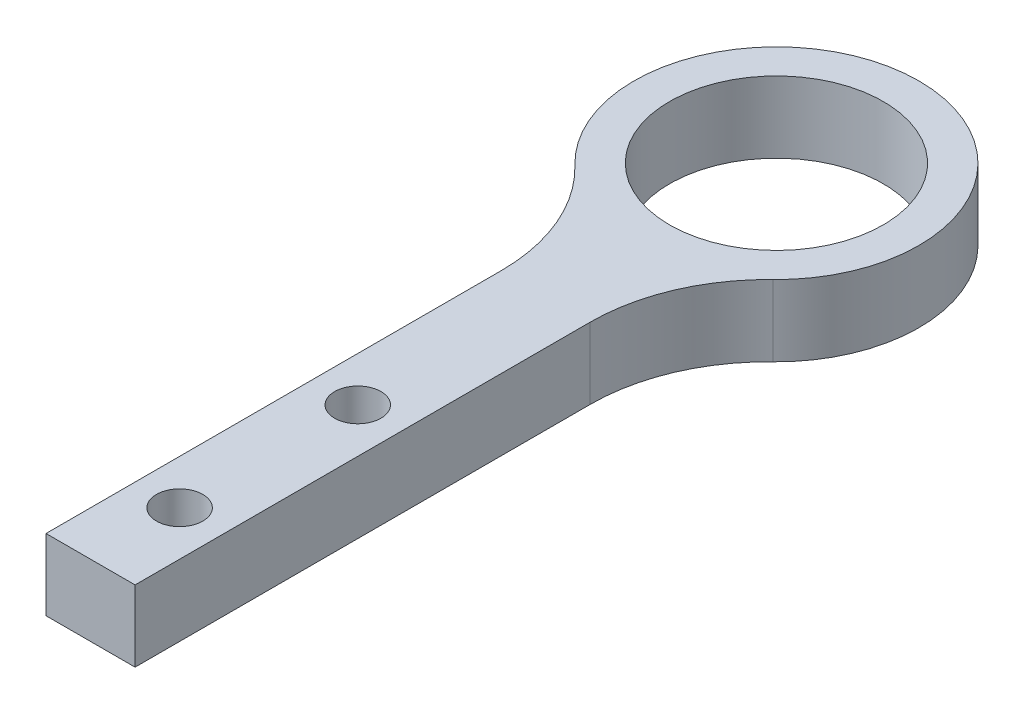
SolidWorks part; units mm, degrees
material "Nylon 101"
ref_plane "Front Plane" through (0, 0, 0) normal (0, 0, 1) x (1, 0, 0)
ref_plane "Top Plane" through (0, 0, 0) normal (0, 1, 0) x (1, 0, 0)
ref_plane "Right Plane" through (0, 0, 0) normal (1, 0, 0) x (0, 0, -1)
sketch "Sketch1" plane through (0, 0, 0) normal (0, 1, 0) x (1, 0, 0)
  line L2 (-2.5, -12.9518) -> (-2.5, -38.5)
  line L3 (-2.5, -38.5) -> (2.5, -38.5)
  line L4 (2.5, -12.9518) -> (2.5, -38.5)
  circle A0 centre (0, 0) radius 6
  arc A1 (5.5556, -5.7564) -> (-5.5556, -5.7564) centre (0, 0) ccw
  arc A4 (5.5556, -5.7564) -> (2.5, -12.9518) centre (12.5, -12.9518) ccw
  arc A5 (-5.5556, -5.7564) -> (-2.5, -12.9518) centre (-12.5, -12.9518) cw
  dimension "D1" = 2
  dimension "D2" = 12
  dimension "D4" = 38.5
  dimension "D5" = 10
  dimension "D3" = 5
extrude "Boss-Extrude1" add sketch "Sketch1" along normal blind 4
sketch "Sketch2" plane through (2.5, 0, 0) normal (0, 1, 0) x (0, 0, -1)
  circle A2 centre (-33.5, 2.5) radius 0.8 construction
  circle A3 centre (-23.5, 2.5) radius 0.8 construction
  circle A4 centre (-33.5, 2.5) radius 0.8
  circle A5 centre (-23.5, 2.5) radius 0.8
hole_wizard "CSK for M2 Flat Head Machine Screw1" positions "Sketch3" profile "Sketch4" countersink size "M2" standard "ANSI Metric" end condition through all
sketch "Sketch3" plane through (0, 0, 0) normal (0, -1, 0) x (-1, 0, 0)
  point P0 (0, -23.5)
  point P3 (0, -33.5)
sketch "Sketch4" plane through (0, 0, 23.5) normal (1, 0, 0) x (0, 0, -1)
  line L0 (0, 0) -> (0, 4)
  line L1 (0, 4) -> (1.3, 4)
  line L2 (1.3, 4) -> (1.3, 0.9)
  line L3 (1.3, 0.9) -> (2.2, 0)
  line L5 (2.2, 0) -> (0, 0)
  line L6 (-1.3, 0.9) -> (-2.2, 0) construction
  line L11 (0, -6.35) -> (0, 107.95) construction
  dimension "Thru Hole Dia." = 2.6
  dimension "Thru Hole Depth" = 4
  dimension "Near C'Sink Dia." = 4.4
  dimension "Near C'Sink Angle" = 90
